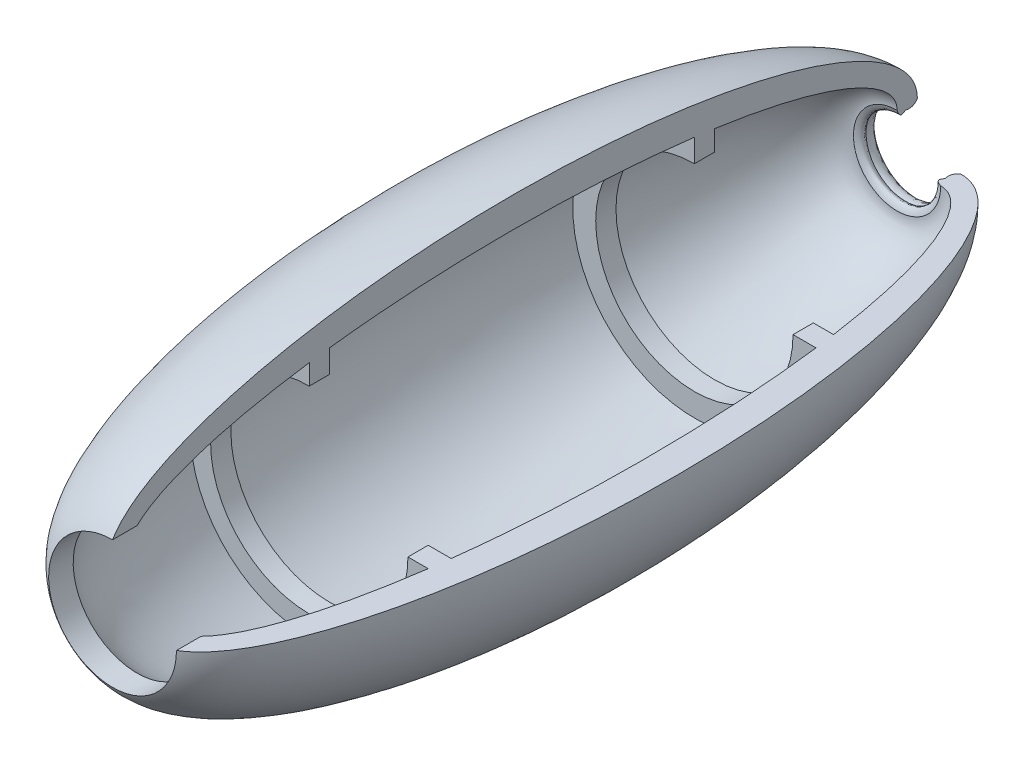
SolidWorks part; units mm, degrees
material "PP Copolymer"
ref_plane "Front Plane" through (0, 0, 0) normal (0, 0, 1) x (1, 0, 0)
ref_plane "Top Plane" through (0, 0, 0) normal (0, 1, 0) x (1, 0, 0)
ref_plane "Right Plane" through (0, 0, 0) normal (1, 0, 0) x (0, 0, -1)
sketch "Sketch1" plane through (0, 0, 0) normal (1, 0, 0) x (0, 0, -1)
  line L0 (-76.3608, 0) -> (18.6392, 0) construction
  line L2 (-79.8934, 5) -> (-73.8371, 5)
  line L3 (-76.3608, 0) -> (-31.3608, 0) construction
  line L4 (-81.3608, -10.77) -> (-81.3608, 5) construction
  line L5 (-31.3608, 48.3812) -> (-31.3608, -52.7647) construction
  line L6 (-81.3608, 5) -> (-73.8371, 5) construction
  line L7 (-31.3608, 0) -> (-26.3608, 0) construction
  line L8 (-26.3608, 0) -> (-26.3608, 48.3812) construction
  line L10 (68.6392, 13.5681) -> (63.6392, 13.5681)
  line L11 (68.6392, 18.5681) -> (68.6392, 13.5681)
  line L12 (-31.3608, 18.5681) -> (-31.3608, 13.5681)
  line L13 (-31.3608, 13.5681) -> (-26.3608, 13.5681)
  line L14 (-26.3608, 19.2321) -> (-26.3608, 13.5681)
  line L15 (63.6392, 19.2321) -> (63.6392, 13.5681)
  line L16 (136.5137, 0) -> (118.6392, 0) construction
  line L17 (118.6392, 0) -> (118.6392, -10.77) construction
  line L18 (18.6392, 61.9848) -> (18.6392, -41.2806) construction
  line L20 (-73.8371, 5) -> (-73.8371, -10.77) construction
  line L21 (68.6392, 0) -> (68.6797, -78.4703) construction
  line L22 (129.7172, -10.77) -> (-99.2263, -10.77) construction
  line L23 (113.6392, 0) -> (-76.3608, 0) construction
  line L24 (-79.8934, 5) -> (-73.8371, 5)
  line L25 (-81.3608, 0) -> (-100.8627, 0) construction
  line L26 (-79.8934, 5) -> (-73.8371, 5)
  ellipse E0 centre (18.6392, 0) end of major axis (-76.3608, 0) minor radius 21.8374 (68.6392, 18.5681) -> (113.6392, 0) cw
  ellipse E2 centre (18.6392, 0) end of major axis (113.6392, 0) minor radius 21.8374 (-31.3608, 18.5681) -> (-73.8371, 5) ccw
  ellipse E3 centre (18.6392, 0) end of major axis (118.6392, 0) minor radius 29.2944 (118.6392, 0) -> (-79.8934, 5) ccw
  ellipse E4 centre (18.6392, 0) end of major axis (113.5988, 0) minor radius 21.8401 (63.6392, 19.2321) -> (-26.3608, 19.2321) ccw
  spline S1 degree 3 poles (118.6392, 0) (117.988, -1.0211) (117.0238, -1.3573) (115.7466, -1.0087) knots 0 0 0 0 0.670729 0.670729 0.670729 0.670729
  spline S2 degree 3 poles (115.7466, -1.0087) (114.8926, -1.6342) (114.2646, -1.9591) (113.6392, 0) knots 0.465469 0.465469 0.465469 0.465469 1 1 1 1
  point P46 (18.6392, 29.2944)
  point P51 (18.6392, 21.8401)
  dimension "D1" = 200
  dimension "D2" = 5
  dimension "D3" = 50
  dimension "D4" = 50
  dimension "D5" = 5
  dimension "D6" = 10.77
  dimension "D7" = 5
  dimension "D8" = 15.77
revolve "Revolve3" add sketch "Sketch1" angle 270 about L22
